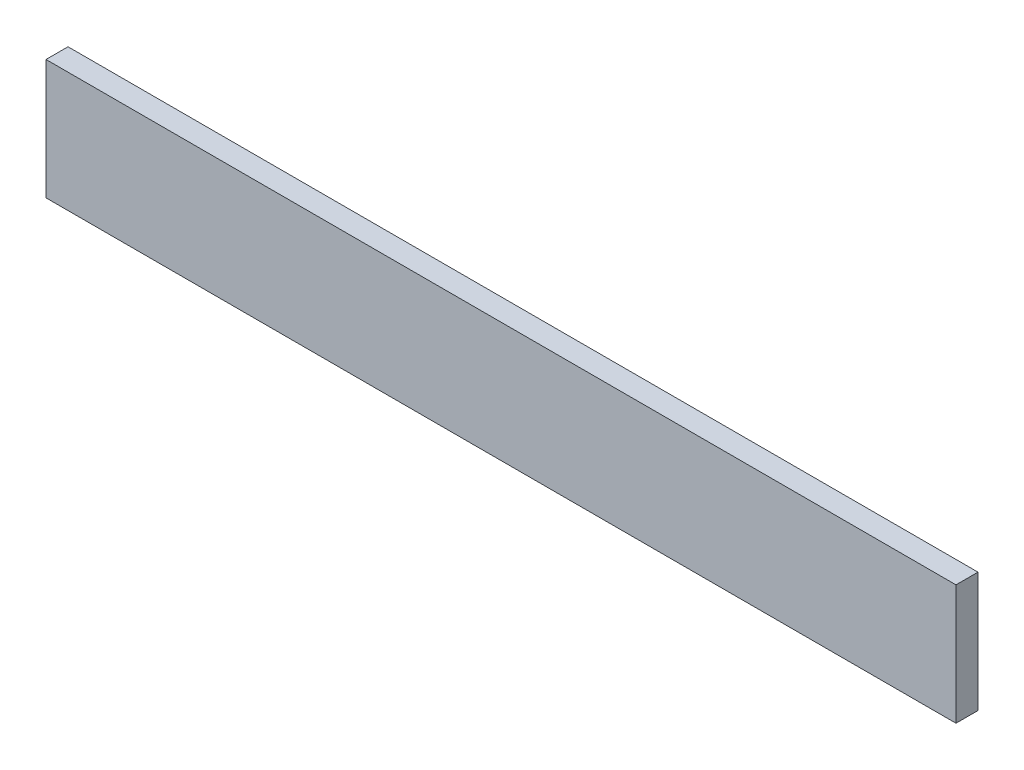
SolidWorks part; units mm, degrees
ref_plane "Front Plane" through (0, 0, 0) normal (0, 0, 1) x (1, 0, 0)
ref_plane "Top Plane" through (0, 0, 0) normal (0, 1, 0) x (1, 0, 0)
ref_plane "Right Plane" through (0, 0, 0) normal (1, 0, 0) x (0, 0, -1)
sketch "Sketch1" plane through (0, 0, 0) normal (0, 0, 1) x (1, 0, 0)
  line L1 (372, -49) -> (-372, -49)
  line L2 (372, -49) -> (372, 49)
  line L3 (372, 49) -> (-372, 49)
  line L4 (-372, -49) -> (-372, 49)
  line L5 (372, -49) -> (-372, 49) construction
  line L6 (372, 49) -> (-372, -49) construction
  point P0 (0, 0)
  dimension "D1" = 98
  dimension "D2" = 744
extrude "Boss-Extrude1" add sketch "Sketch1" along normal blind 18
equation "\"H_DSP\"=18"
equation "\"D1@Boss-Extrude1\"=\"H_DSP\""
